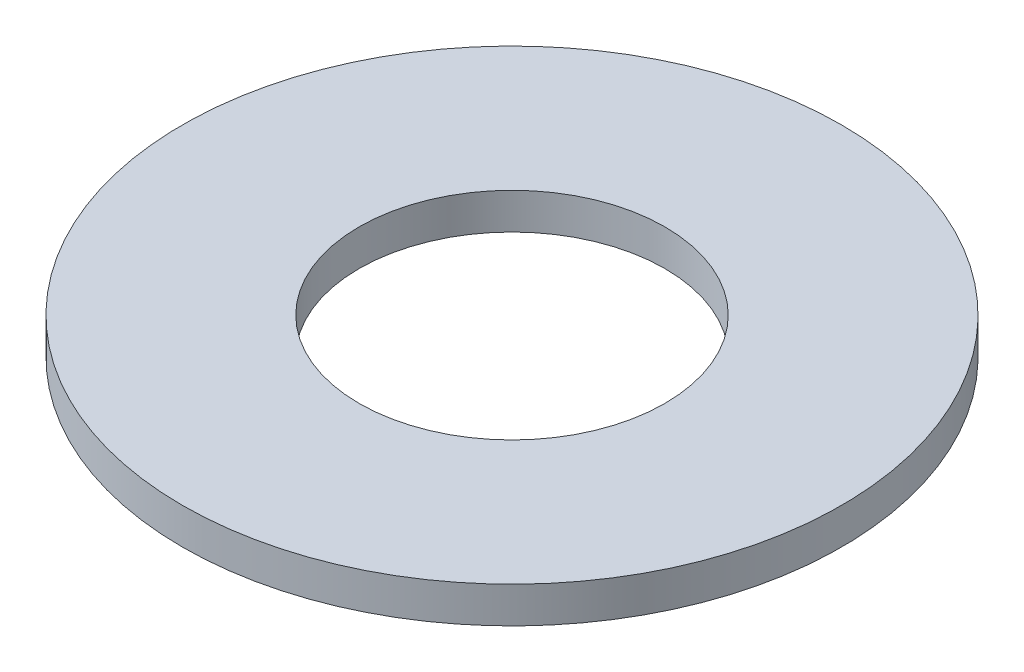
SolidWorks part; units mm, degrees
material "Alloy Steel (SS)"
ref_plane "Front Plane" through (0, 0, 0) normal (0, 0, 1) x (1, 0, 0)
ref_plane "Top Plane" through (0, 0, 0) normal (0, 1, 0) x (1, 0, 0)
ref_plane "Right Plane" through (0, 0, 0) normal (1, 0, 0) x (0, 0, -1)
sketch "Sketch1" plane through (0, 0, 0) normal (0, 1, 0) x (1, 0, 0)
  circle A0 centre (0, 0) radius 5.5562
  dimension "OD" = 11.1125
extrude "Boss-Extrude1" add sketch "Sketch1" along normal blind 0.6096
sketch "Sketch5" plane through (0, 0.6096, 0) normal (0, 1, 0) x (-1, 0, 0)
  circle A0 centre (0, 0) radius 2.5781
  dimension "ID" = 5.1562
extrude "Cut-Extrude1" cut sketch "Sketch5" against normal through all
